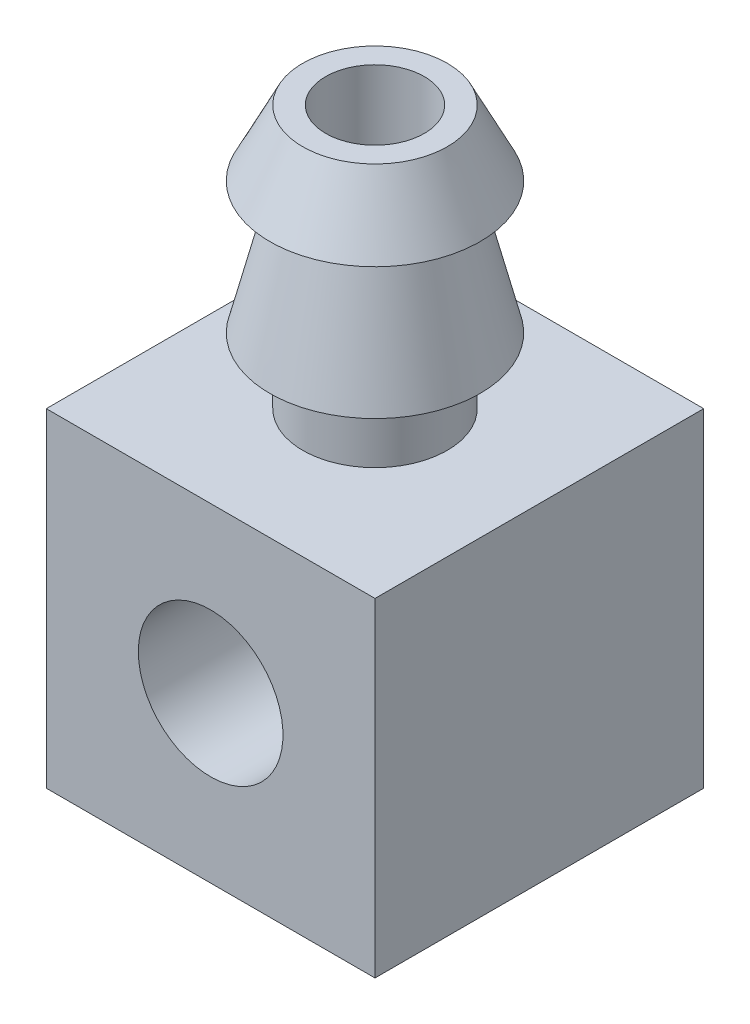
SolidWorks part; units mm, degrees
ref_plane "Front Plane" through (0, 0, 0) normal (0, 0, 1) x (1, 0, 0)
ref_plane "Top Plane" through (0, 0, 0) normal (0, 1, 0) x (1, 0, 0)
ref_plane "Right Plane" through (0, 0, 0) normal (1, 0, 0) x (0, 0, -1)
sketch "Sketch1" plane through (0, 0, 0) normal (0, 0, 1) x (1, 0, 0)
  line L1 (-2.5, -2.5) -> (2.5, -2.5)
  line L2 (-2.5, -2.5) -> (-2.5, 2.5)
  line L3 (-2.5, 2.5) -> (2.5, 2.5)
  line L4 (2.5, -2.5) -> (2.5, 2.5)
  line L5 (-2.5, -2.5) -> (2.5, 2.5) construction
  line L6 (-2.5, 2.5) -> (2.5, -2.5) construction
  point P0 (0, 0)
  dimension "D1" = 5
  dimension "D2" = 5
extrude "Boss-Extrude1" add sketch "Sketch1" along normal blind 5
sketch "Sketch2" plane through (0, 0, 0) normal (1, 0, 0) x (0, 0, -1)
  line L0 (-2.5, 2.5) -> (-2.5, 6.5)
  line L1 (-5, 2.5) -> (0, 2.5) construction
  line L2 (-2.5, 2.5) -> (-3.6, 2.5)
  line L3 (-3.6, 2.5) -> (-3.6, 3.5)
  line L4 (-3.6, 3.5) -> (-4.1, 3.5)
  line L5 (-4.1, 3.5) -> (-3.6, 5.5)
  line L6 (-3.6, 5.5) -> (-4.1, 5.5)
  line L7 (-4.1, 5.5) -> (-3.6, 6.5)
  line L8 (-3.6, 6.5) -> (-2.5, 6.5)
  line L9 (-3.6, 6.5) -> (-3.6, 2.5) construction
  dimension "D1" = 0.5
  dimension "D2" = 0.5
  dimension "D3" = 1
  dimension "D4" = 2
  dimension "D5" = 1
  dimension "D6" = 1.1
revolve "Revolve1" add sketch "Sketch2" angle 360 about L0
sketch "Sketch5" plane through (0, 6.5, 0) normal (0, 1, 0) x (1, 0, 0)
  circle A0 centre (0, -2.5) radius 0.75
  dimension "D1" = 1.5
extrude "Cut-Extrude1" cut sketch "Sketch5" against normal blind 8
sketch "Sketch6" plane through (0, 0, 0) normal (0, 0, -1) x (-1, 0, 0)
  circle A0 centre (0, 0) radius 1.1
  dimension "D1" = 2.2
extrude "Cut-Extrude2" cut sketch "Sketch6" against normal blind 8 contours A0
